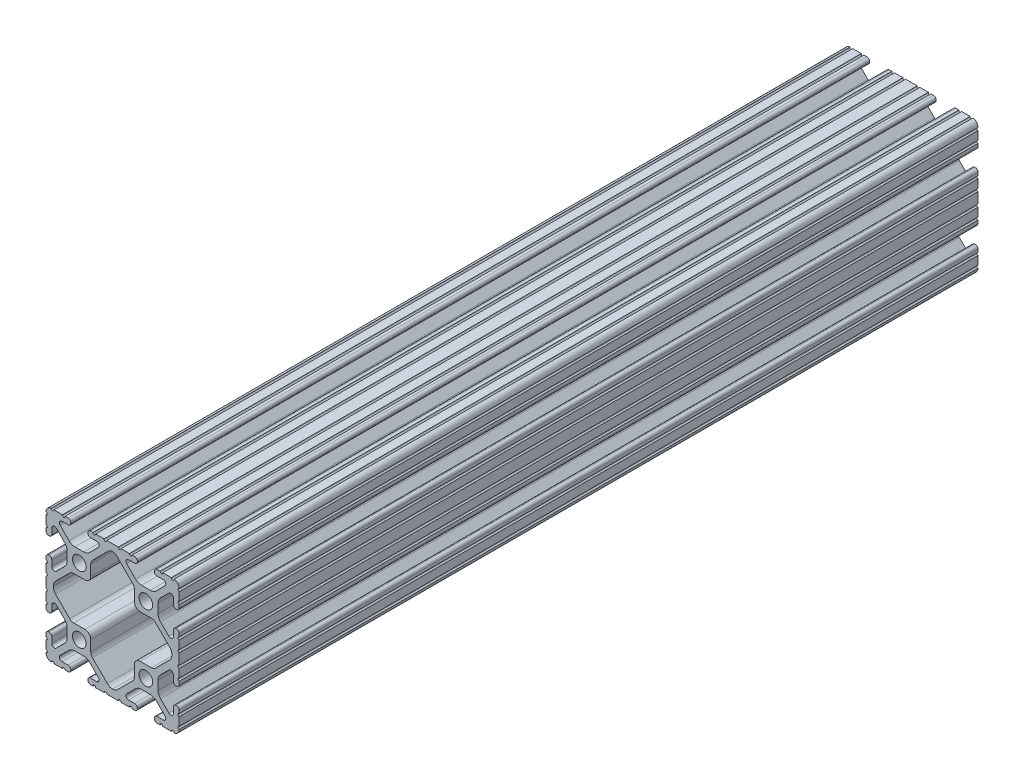
SolidWorks part; units mm, degrees
material "6061 Alloy"
ref_plane "Front Plane" through (0, 0, 0) normal (0, 0, 1) x (1, 0, 0)
ref_plane "Top Plane" through (0, 0, 0) normal (0, 1, 0) x (1, 0, 0)
ref_plane "Right Plane" through (0, 0, 0) normal (1, 0, 0) x (0, 0, -1)
sketch "Sketch1" plane through (0, 0, 0) normal (0, 0, 1) x (1, 0, 0)
  line L1 (-2.2101, -25.4) -> (2.2101, -25.4)
  line L2 (12.7883, 29.5847) -> (12.7883, -24.0404) construction
  line L3 (7.4579, -25.4) -> (8.4051, -25.4)
  line L4 (9.4615, -24.3587) -> (9.4615, -24.2315)
  line L5 (6.0878, -23.1902) -> (8.4051, -23.1902)
  line L6 (-12.7, -45.1098) -> (-12.7, 28.7522) construction
  line L7 (-25.8162, -12.7) -> (-12.7, -12.7) construction
  line L8 (0, 25.5922) -> (0, -25.5922) construction
  line L9 (-22.8238, 0) -> (0, 0) construction
  line L10 (8.763, -18.1257) -> (5.388, -21.5008)
  line L11 (14.3919, -17.1958) -> (11.0081, -17.1958)
  line L12 (20.012, -21.5008) -> (16.637, -18.1257)
  line L13 (16.9799, -23.1901) -> (19.2977, -23.1901)
  line L14 (15.9385, -24.3585) -> (15.9385, -24.2315)
  line L15 (16.9949, -25.4) -> (18.134, -25.4)
  line L16 (19.1384, -25.4) -> (20.1295, -25.4)
  line L17 (20.1295, -25.4) -> (22.4132, -25.4)
  line L18 (23.4501, -25.4) -> (23.4176, -25.4)
  line L19 (25.4, -23.294) -> (25.4, -23.2686)
  line L20 (25.4, -22.2526) -> (25.4, -21.1604)
  line L21 (25.4, -21.1604) -> (25.4, -19.0252)
  line L22 (25.4, -18.0092) -> (25.4, -16.916)
  line L23 (24.2316, -15.8746) -> (24.3586, -15.8746)
  line L24 (23.1902, -19.101) -> (23.1902, -16.916)
  line L25 (18.2781, -16.6418) -> (21.4558, -19.8194)
  line L26 (17.3482, -11.0035) -> (17.3482, -14.3967)
  line L27 (21.4566, -5.5875) -> (18.2808, -8.7557)
  line L28 (23.1902, -8.484) -> (23.1902, -6.3068)
  line L29 (-1.9878, -21.7759) -> (-7.684, -16.0797)
  line L30 (10.541, 8.1792) -> (14.8161, 8.1792)
  line L31 (-16.3772, -7.5334) -> (-21.7734, -2.1502)
  line L32 (24.3586, -9.5254) -> (24.2316, -9.5254)
  line L33 (25.4, -8.484) -> (25.4, -7.3277)
  line L34 (25.4, -3.0843) -> (25.4, -6.3117)
  line L35 (-25.4, 6.3117) -> (-25.4, 3.0843)
  line L36 (-22.6314, 0.0822) -> (-22.6314, -0.0822)
  line L37 (16.3772, -7.5334) -> (21.7734, -2.1502)
  line L38 (-14.8165, -8.1788) -> (-10.541, -8.1788)
  line L39 (12.7, -12.7) -> (25.8162, -12.7) construction
  line L40 (1.9878, -21.7759) -> (7.684, -16.0797)
  line L41 (3.2145, -25.4) -> (6.4535, -25.4)
  line L42 (22.6314, 0.0822) -> (22.6314, -0.0822)
  line L43 (-17.3482, -11.0035) -> (-17.3482, -14.3967)
  line L44 (25.4, 6.3117) -> (25.4, 3.0843)
  line L45 (-23.4501, -25.4) -> (-23.4176, -25.4)
  line L46 (-5.2705, 25.4) -> (-3.2145, 25.4)
  line L47 (-6.4535, 25.4) -> (-5.2705, 25.4)
  line L48 (-8.4051, 25.4) -> (-7.4579, 25.4)
  line L49 (-9.4615, 24.2315) -> (-9.4615, 24.3587)
  line L50 (-8.4051, 23.1902) -> (-6.0878, 23.1902)
  line L51 (-8.763, 18.1257) -> (-5.388, 21.5008)
  line L52 (-14.3919, 17.1958) -> (-11.0081, 17.1958)
  line L53 (-20.012, 21.5008) -> (-16.637, 18.1257)
  line L54 (-19.2977, 23.1901) -> (-16.9799, 23.1901)
  line L55 (-15.9385, 24.3585) -> (-15.9385, 24.2315)
  line L56 (-18.134, 25.4) -> (-16.9949, 25.4)
  line L57 (-20.1295, 25.4) -> (-19.1384, 25.4)
  line L58 (-22.4132, 25.4) -> (-20.1295, 25.4)
  line L59 (-23.4501, 25.4) -> (-23.4176, 25.4)
  line L60 (-25.4, 23.2686) -> (-25.4, 23.294)
  line L61 (-25.4, 21.1604) -> (-25.4, 22.2526)
  line L62 (-25.4, 19.0252) -> (-25.4, 21.1604)
  line L63 (-25.4, 16.916) -> (-25.4, 18.0092)
  line L64 (-24.3586, 15.8746) -> (-24.2316, 15.8746)
  line L65 (-23.1902, 19.101) -> (-23.1902, 16.916)
  line L66 (-18.2781, 16.6418) -> (-21.4558, 19.8194)
  line L67 (-17.3482, 11.0035) -> (-17.3482, 14.3967)
  line L68 (-21.4566, 5.5875) -> (-18.2808, 8.7557)
  line L69 (-23.1902, 6.3068) -> (-23.1902, 8.484)
  line L70 (-24.3586, 9.5254) -> (-24.2316, 9.5254)
  line L71 (-25.4, 7.3277) -> (-25.4, 8.484)
  line L74 (-14.8165, 8.1788) -> (-10.541, 8.1788)
  line L75 (-8.3312, 10.3886) -> (-8.3312, 14.5171)
  line L76 (3.2145, 25.4) -> (6.4535, 25.4)
  line L77 (1.7956, 21.9681) -> (7.684, 16.0797)
  line L78 (12.7, 12.7) -> (25.8162, 12.7) construction
  line L80 (16.3768, 7.5339) -> (21.7734, 2.1502)
  line L82 (25.4, 2.0683) -> (25.4, -2.0683)
  line L83 (8.3312, 12.7001) -> (8.3312, 10.389)
  line L84 (25.4, 7.3277) -> (25.4, 8.484)
  line L85 (24.3586, 9.5254) -> (24.2316, 9.5254)
  line L86 (-16.3772, 7.5334) -> (-21.7734, 2.1502)
  line L88 (-1.7956, 21.9681) -> (-7.684, 16.0797)
  line L89 (23.1902, 6.3068) -> (23.1902, 8.484)
  line L90 (21.4566, 5.5875) -> (18.2808, 8.7557)
  line L91 (17.3482, 11.0035) -> (17.3482, 14.3967)
  line L92 (18.2781, 16.6418) -> (21.4558, 19.8194)
  line L93 (23.1902, 19.101) -> (23.1902, 16.916)
  line L94 (24.2316, 15.8746) -> (24.3586, 15.8746)
  line L95 (25.4, 16.916) -> (25.4, 18.0092)
  line L96 (25.4, 19.0252) -> (25.4, 21.1604)
  line L97 (25.4, 21.1604) -> (25.4, 22.2526)
  line L98 (25.4, 23.2686) -> (25.4, 23.294)
  line L99 (23.4501, 25.4) -> (23.4176, 25.4)
  line L100 (20.1295, 25.4) -> (22.4132, 25.4)
  line L101 (19.1384, 25.4) -> (20.1295, 25.4)
  line L102 (16.9949, 25.4) -> (18.134, 25.4)
  line L103 (15.9385, 24.3585) -> (15.9385, 24.2315)
  line L104 (16.9799, 23.1901) -> (19.2977, 23.1901)
  line L105 (20.012, 21.5008) -> (16.637, 18.1257)
  line L106 (14.3919, 17.1958) -> (11.0081, 17.1958)
  line L107 (8.763, 18.1257) -> (5.388, 21.5008)
  line L108 (-25.8162, 12.7) -> (-12.7, 12.7) construction
  line L109 (6.0878, 23.1902) -> (8.4051, 23.1902)
  line L110 (9.4615, 24.2315) -> (9.4615, 24.3587)
  line L111 (7.4579, 25.4) -> (8.4051, 25.4)
  line L112 (8.3312, 12.7001) -> (8.3312, 14.5171)
  line L113 (-2.2101, 25.4) -> (2.2101, 25.4)
  line L114 (-22.4132, -25.4) -> (-20.1295, -25.4)
  line L115 (-20.1295, -25.4) -> (-19.1384, -25.4)
  line L116 (-18.134, -25.4) -> (-16.9949, -25.4)
  line L117 (-8.4051, -25.4) -> (-7.4579, -25.4)
  line L118 (-6.4535, -25.4) -> (-5.2705, -25.4)
  line L119 (-5.2705, -25.4) -> (-3.2145, -25.4)
  line L120 (-19.2977, -23.1901) -> (-16.9799, -23.1901)
  line L121 (-8.4051, -23.1902) -> (-6.0878, -23.1902)
  line L122 (-8.3312, -14.5171) -> (-8.3312, -10.3886)
  line L123 (-14.3919, -17.1958) -> (-11.0081, -17.1958)
  line L125 (-24.3586, -15.8746) -> (-24.2316, -15.8746)
  line L127 (-24.3586, -9.5254) -> (-24.2316, -9.5254)
  line L128 (14.8165, -8.1788) -> (10.541, -8.1788)
  line L129 (8.3312, -10.3886) -> (8.3312, -14.5171)
  line L130 (-9.4615, -24.3587) -> (-9.4615, -24.2315)
  line L132 (-15.9385, -24.3585) -> (-15.9385, -24.2315)
  line L134 (-25.4, -23.294) -> (-25.4, -23.2686)
  line L135 (-25.4, -22.2526) -> (-25.4, -21.1604)
  line L136 (-25.4, -21.1604) -> (-25.4, -19.0252)
  line L137 (-25.4, -18.0092) -> (-25.4, -16.916)
  line L138 (-25.4, -8.484) -> (-25.4, -7.3277)
  line L139 (-25.4, -6.3117) -> (-25.4, -4.1765)
  line L140 (-25.4, -4.1765) -> (-25.4, -3.0843)
  line L141 (-25.4, -2.0683) -> (-25.4, 2.0683)
  line L143 (-23.1902, -19.101) -> (-23.1902, -16.916)
  line L144 (-23.1902, -8.484) -> (-23.1902, -6.3068)
  line L198 (-21.4566, -5.5875) -> (-18.2808, -8.7557)
  line L200 (-18.2781, -16.6418) -> (-21.4558, -19.8194)
  line L213 (-20.012, -21.5008) -> (-16.637, -18.1257)
  line L215 (-8.763, -18.1257) -> (-5.388, -21.5008)
  arc A0 (6.4535, -25.4) -> (7.4579, -25.4) centre (6.9557, -25.3234) cw
  arc A1 (9.4615, -24.3587) -> (8.4051, -25.4) centre (8.4201, -24.3587) cw
  arc A2 (8.4051, -23.1902) -> (9.4615, -24.2315) centre (8.4201, -24.2315) cw
  arc A3 (6.0878, -23.1902) -> (5.388, -21.5008) centre (6.0878, -22.2006) cw
  arc A4 (8.763, -18.1257) -> (11.0081, -17.1958) centre (11.0081, -20.3708) cw
  arc A5 (14.3919, -17.1958) -> (16.637, -18.1257) centre (14.3919, -20.3708) cw
  arc A6 (20.012, -21.5008) -> (19.2977, -23.1901) centre (19.3122, -22.2006) cw
  arc A7 (15.9385, -24.2315) -> (16.9799, -23.1901) centre (16.9799, -24.2315) cw
  arc A8 (16.9949, -25.4) -> (15.9385, -24.3585) centre (16.9799, -24.3587) cw
  arc A9 (18.134, -25.4) -> (19.1384, -25.4) centre (18.6362, -25.3234) cw
  arc A10 (22.4132, -25.4) -> (23.4176, -25.4) centre (22.9154, -25.3234) cw
  arc A11 (25.4, -23.294) -> (23.4501, -25.4) centre (23.2918, -23.2977) cw
  arc A12 (25.4, -23.2686) -> (25.4, -22.2526) centre (25.4, -22.7606) cw
  arc A13 (25.4, -19.0252) -> (25.4, -18.0092) centre (25.4, -18.5172) cw
  arc A14 (24.3586, -15.8746) -> (25.4, -16.916) centre (24.3586, -16.916) cw
  arc A15 (23.1902, -16.916) -> (24.2316, -15.8746) centre (24.2316, -16.916) cw
  arc A16 (23.1902, -19.101) -> (21.4558, -19.8194) centre (22.1742, -19.101) cw
  arc A17 (18.2781, -16.6418) -> (17.3482, -14.3967) centre (20.5232, -14.3967) cw
  arc A18 (17.3482, -11.0035) -> (18.2808, -8.7557) centre (20.5232, -11.0035) cw
  arc A19 (0, -22.6304) -> (-1.9878, -21.7759) centre (0.0777, -19.7104) cw
  arc A20 (21.4566, -5.5875) -> (23.1902, -6.3068) centre (22.1742, -6.3068) cw
  arc A21 (24.2316, -9.5254) -> (23.1902, -8.484) centre (24.2316, -8.484) cw
  arc A22 (-14.8165, -8.1788) -> (-16.3772, -7.5334) centre (-14.8165, -5.969) cw
  arc A23 (-8.3312, -10.3886) -> (-10.541, -8.1788) centre (-10.541, -10.3886) ccw
  arc A24 (25.4, -8.484) -> (24.3586, -9.5254) centre (24.3586, -8.484) cw
  arc A25 (25.4, -7.3277) -> (25.4, -6.3117) centre (25.4, -6.8197) cw
  arc A26 (-22.6314, 0.0822) -> (-21.7734, 2.1502) centre (-19.7104, 0.0822) cw
  arc A27 (-7.684, -16.0797) -> (-8.3312, -14.5171) centre (-6.1214, -14.5171) cw
  arc A28 (-8.3312, 10.3886) -> (-10.541, 8.1788) centre (-10.541, 10.3886) cw
  circle A29 centre (12.7, -12.7) radius 2.6035
  arc A30 (14.8165, -8.1788) -> (16.3772, -7.5334) centre (14.8165, -5.969) ccw
  arc A31 (8.3312, -10.3886) -> (10.541, -8.1788) centre (10.541, -10.3886) cw
  arc A32 (8.3312, -14.5171) -> (7.684, -16.0797) centre (6.1214, -14.5171) cw
  arc A33 (0, -22.6304) -> (1.9878, -21.7759) centre (-0.0777, -19.7104) ccw
  arc A34 (2.2101, -25.4) -> (3.2145, -25.4) centre (2.7123, -25.3234) cw
  arc A35 (25.4, -3.0843) -> (25.4, -2.0683) centre (25.4, -2.5763) cw
  arc A36 (22.6314, 0.0822) -> (21.7734, 2.1502) centre (19.7104, 0.0822) ccw
  circle A37 centre (-12.7, -12.7) radius 2.6035
  arc A38 (-2.2101, 25.4) -> (-3.2145, 25.4) centre (-2.7123, 25.3234) cw
  arc A39 (-6.4535, 25.4) -> (-7.4579, 25.4) centre (-6.9557, 25.3234) cw
  arc A40 (-9.4615, 24.3587) -> (-8.4051, 25.4) centre (-8.4201, 24.3587) cw
  arc A41 (-8.4051, 23.1902) -> (-9.4615, 24.2315) centre (-8.4201, 24.2315) cw
  arc A42 (-6.0878, 23.1902) -> (-5.388, 21.5008) centre (-6.0878, 22.2006) cw
  arc A43 (-8.763, 18.1257) -> (-11.0081, 17.1958) centre (-11.0081, 20.3708) cw
  arc A44 (-14.3919, 17.1958) -> (-16.637, 18.1257) centre (-14.3919, 20.3708) cw
  arc A45 (-20.012, 21.5008) -> (-19.2977, 23.1901) centre (-19.3122, 22.2006) cw
  arc A46 (-15.9385, 24.2315) -> (-16.9799, 23.1901) centre (-16.9799, 24.2315) cw
  arc A47 (-16.9949, 25.4) -> (-15.9385, 24.3585) centre (-16.9799, 24.3587) cw
  arc A48 (-18.134, 25.4) -> (-19.1384, 25.4) centre (-18.6362, 25.3234) cw
  arc A49 (-22.4132, 25.4) -> (-23.4176, 25.4) centre (-22.9154, 25.3234) cw
  arc A50 (-25.4, 23.294) -> (-23.4501, 25.4) centre (-23.2918, 23.2977) cw
  arc A51 (-25.4, 23.2686) -> (-25.4, 22.2526) centre (-25.4, 22.7606) cw
  arc A52 (-25.4, 19.0252) -> (-25.4, 18.0092) centre (-25.4, 18.5172) cw
  arc A53 (-24.3586, 15.8746) -> (-25.4, 16.916) centre (-24.3586, 16.916) cw
  arc A54 (-23.1902, 16.916) -> (-24.2316, 15.8746) centre (-24.2316, 16.916) cw
  arc A55 (-23.1902, 19.101) -> (-21.4558, 19.8194) centre (-22.1742, 19.101) cw
  arc A56 (-18.2781, 16.6418) -> (-17.3482, 14.3967) centre (-20.5232, 14.3967) cw
  arc A57 (-17.3482, 11.0035) -> (-18.2808, 8.7557) centre (-20.5232, 11.0035) cw
  arc A58 (-21.4566, 5.5875) -> (-23.1902, 6.3068) centre (-22.1742, 6.3068) cw
  arc A59 (-24.2316, 9.5254) -> (-23.1902, 8.484) centre (-24.2316, 8.484) cw
  arc A60 (-25.4, 8.484) -> (-24.3586, 9.5254) centre (-24.3586, 8.484) cw
  arc A61 (-25.4, 7.3277) -> (-25.4, 6.3117) centre (-25.4, 6.8197) cw
  arc A62 (-25.4, 3.0843) -> (-25.4, 2.0683) centre (-25.4, 2.5763) cw
  circle A63 centre (-12.7, 12.7) radius 2.6035
  arc A64 (-8.3312, 14.5171) -> (-7.684, 16.0797) centre (-6.1214, 14.5171) cw
  arc A65 (2.2101, 25.4) -> (3.2145, 25.4) centre (2.7123, 25.3234) ccw
  arc A66 (0, 22.8111) -> (-1.7956, 21.9681) centre (0.2699, 19.9026) ccw
  arc A67 (8.3312, 14.5171) -> (7.684, 16.0797) centre (6.1214, 14.5171) ccw
  arc A68 (10.541, 8.1792) -> (8.3312, 10.389) centre (10.541, 10.389) cw
  arc A69 (14.8161, 8.1792) -> (16.3768, 7.5339) centre (14.8161, 5.9694) cw
  circle A70 centre (12.7, 12.7) radius 2.6035
  arc A71 (25.4, 3.0843) -> (25.4, 2.0683) centre (25.4, 2.5763) ccw
  arc A72 (-14.8165, 8.1788) -> (-16.3772, 7.5334) centre (-14.8165, 5.969) ccw
  arc A73 (25.4, 7.3277) -> (25.4, 6.3117) centre (25.4, 6.8197) ccw
  arc A74 (25.4, 8.484) -> (24.3586, 9.5254) centre (24.3586, 8.484) ccw
  arc A75 (22.6314, -0.0822) -> (21.7734, -2.1502) centre (19.7104, -0.0822) cw
  arc A76 (-22.6314, -0.0822) -> (-21.7734, -2.1502) centre (-19.7104, -0.0822) ccw
  arc A77 (24.2316, 9.5254) -> (23.1902, 8.484) centre (24.2316, 8.484) ccw
  arc A78 (21.4566, 5.5875) -> (23.1902, 6.3068) centre (22.1742, 6.3068) ccw
  arc A79 (1.7956, 21.9681) -> (0, 22.8111) centre (-0.2699, 19.9026) ccw
  arc A80 (17.3482, 11.0035) -> (18.2808, 8.7557) centre (20.5232, 11.0035) ccw
  arc A81 (18.2781, 16.6418) -> (17.3482, 14.3967) centre (20.5232, 14.3967) ccw
  arc A82 (23.1902, 19.101) -> (21.4558, 19.8194) centre (22.1742, 19.101) ccw
  arc A83 (23.1902, 16.916) -> (24.2316, 15.8746) centre (24.2316, 16.916) ccw
  arc A84 (24.3586, 15.8746) -> (25.4, 16.916) centre (24.3586, 16.916) ccw
  arc A85 (25.4, 19.0252) -> (25.4, 18.0092) centre (25.4, 18.5172) ccw
  arc A86 (25.4, 23.2686) -> (25.4, 22.2526) centre (25.4, 22.7606) ccw
  arc A87 (25.4, 23.294) -> (23.4501, 25.4) centre (23.2918, 23.2977) ccw
  arc A88 (22.4132, 25.4) -> (23.4176, 25.4) centre (22.9154, 25.3234) ccw
  arc A89 (18.134, 25.4) -> (19.1384, 25.4) centre (18.6362, 25.3234) ccw
  arc A90 (16.9949, 25.4) -> (15.9385, 24.3585) centre (16.9799, 24.3587) ccw
  arc A91 (15.9385, 24.2315) -> (16.9799, 23.1901) centre (16.9799, 24.2315) ccw
  arc A92 (20.012, 21.5008) -> (19.2977, 23.1901) centre (19.3122, 22.2006) ccw
  arc A93 (14.3919, 17.1958) -> (16.637, 18.1257) centre (14.3919, 20.3708) ccw
  arc A94 (8.763, 18.1257) -> (11.0081, 17.1958) centre (11.0081, 20.3708) ccw
  arc A95 (6.0878, 23.1902) -> (5.388, 21.5008) centre (6.0878, 22.2006) ccw
  arc A96 (8.4051, 23.1902) -> (9.4615, 24.2315) centre (8.4201, 24.2315) ccw
  arc A97 (9.4615, 24.3587) -> (8.4051, 25.4) centre (8.4201, 24.3587) ccw
  arc A98 (6.4535, 25.4) -> (7.4579, 25.4) centre (6.9557, 25.3234) ccw
  arc A182 (-25.4, -3.0843) -> (-25.4, -2.0683) centre (-25.4, -2.5763) ccw
  arc A183 (-25.4, -7.3277) -> (-25.4, -6.3117) centre (-25.4, -6.8197) ccw
  arc A184 (-25.4, -8.484) -> (-24.3586, -9.5254) centre (-24.3586, -8.484) ccw
  arc A185 (-24.2316, -9.5254) -> (-23.1902, -8.484) centre (-24.2316, -8.484) ccw
  arc A186 (-21.4566, -5.5875) -> (-23.1902, -6.3068) centre (-22.1742, -6.3068) ccw
  arc A187 (-17.3482, -11.0035) -> (-18.2808, -8.7557) centre (-20.5232, -11.0035) ccw
  arc A188 (-18.2781, -16.6418) -> (-17.3482, -14.3967) centre (-20.5232, -14.3967) ccw
  arc A189 (-23.1902, -19.101) -> (-21.4558, -19.8194) centre (-22.1742, -19.101) ccw
  arc A190 (-23.1902, -16.916) -> (-24.2316, -15.8746) centre (-24.2316, -16.916) ccw
  arc A191 (-24.3586, -15.8746) -> (-25.4, -16.916) centre (-24.3586, -16.916) ccw
  arc A192 (-25.4, -19.0252) -> (-25.4, -18.0092) centre (-25.4, -18.5172) ccw
  arc A193 (-25.4, -23.2686) -> (-25.4, -22.2526) centre (-25.4, -22.7606) ccw
  arc A194 (-25.4, -23.294) -> (-23.4501, -25.4) centre (-23.2918, -23.2977) ccw
  arc A195 (-22.4132, -25.4) -> (-23.4176, -25.4) centre (-22.9154, -25.3234) ccw
  arc A196 (-18.134, -25.4) -> (-19.1384, -25.4) centre (-18.6362, -25.3234) ccw
  arc A197 (-16.9949, -25.4) -> (-15.9385, -24.3585) centre (-16.9799, -24.3587) ccw
  arc A198 (-15.9385, -24.2315) -> (-16.9799, -23.1901) centre (-16.9799, -24.2315) ccw
  arc A199 (-20.012, -21.5008) -> (-19.2977, -23.1901) centre (-19.3122, -22.2006) ccw
  arc A200 (-14.3919, -17.1958) -> (-16.637, -18.1257) centre (-14.3919, -20.3708) ccw
  arc A201 (-8.763, -18.1257) -> (-11.0081, -17.1958) centre (-11.0081, -20.3708) ccw
  arc A202 (-6.0878, -23.1902) -> (-5.388, -21.5008) centre (-6.0878, -22.2006) ccw
  arc A203 (-8.4051, -23.1902) -> (-9.4615, -24.2315) centre (-8.4201, -24.2315) ccw
  arc A204 (-9.4615, -24.3587) -> (-8.4051, -25.4) centre (-8.4201, -24.3587) ccw
  arc A205 (-6.4535, -25.4) -> (-7.4579, -25.4) centre (-6.9557, -25.3234) ccw
  arc A206 (-2.2101, -25.4) -> (-3.2145, -25.4) centre (-2.7123, -25.3234) ccw
  point P397 (16.6343, 7.277)
  dimension "D1" = 5.207
  dimension "D3" = 6.477
  dimension "D4" = 8.2042
  dimension "D5" = 25.4
  dimension "D10" = 12.7
  dimension "D8" = 2.2098
  dimension "D9" = 2.2098
  dimension "D12" = 2.2098
  dimension "D13" = 2.2098
  dimension "D14" = 2.2098
  dimension "D15" = 2.2098
  dimension "D16" = 2.921
  dimension "D17" = 2.921
  dimension "D18" = 2.921
  dimension "D19" = 2.921
  dimension "D20" = 2.921
  dimension "D21" = 2.921
  dimension "D2" = 2.2098
  dimension "D6" = 14.859
  dimension "D7" = 50.8
  dimension "D11" = 2.2098
extrude "Extrude1" add sketch "Sketch1" against normal blind 304.8
